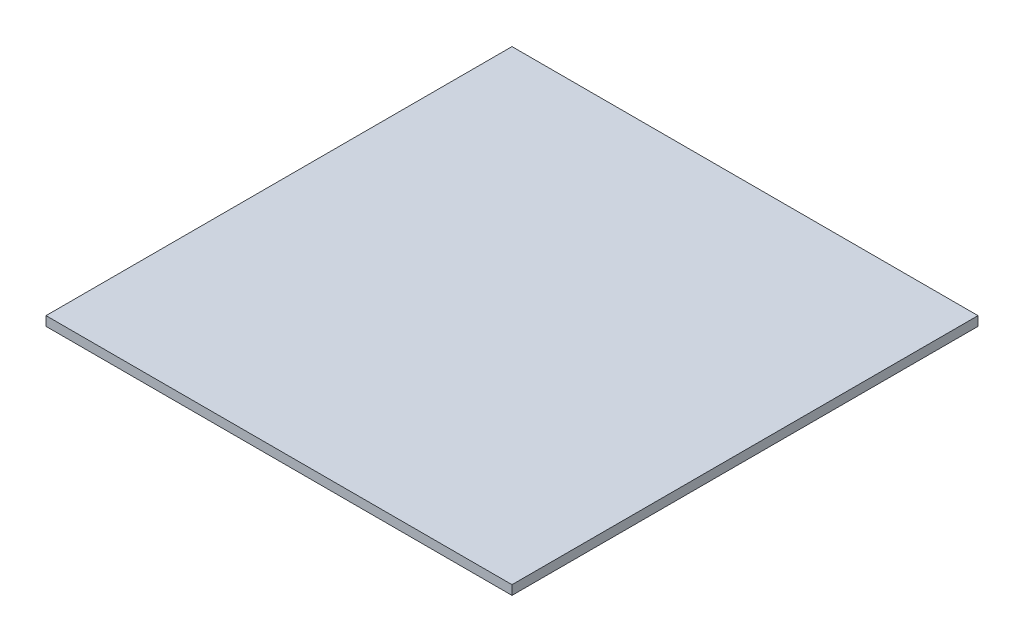
SolidWorks part; units mm, degrees
ref_plane "Vorne" through (0, 0, 0) normal (0, 0, 1) x (1, 0, 0)
ref_plane "Oben" through (0, 0, 0) normal (0, 1, 0) x (1, 0, 0)
ref_plane "Rechts" through (0, 0, 0) normal (1, 0, 0) x (0, 0, -1)
sketch "Skizze2" plane through (0, 0, 0) normal (0, 1, 0) x (1, 0, 0)
  line L1 (-500, -500) -> (500, -500)
  line L2 (-500, -500) -> (-500, 500)
  line L3 (-500, 500) -> (500, 500)
  line L4 (500, -500) -> (500, 500)
  line L5 (-500, -500) -> (500, 500) construction
  line L6 (-500, 500) -> (500, -500) construction
  point P0 (0, 0)
  dimension "D1" = 1000
  dimension "D2" = 1000
extrude "Aufsatz-Linear austragen1" add sketch "Skizze2" along normal blind 20
sketch "Skizze3" [suppressed] plane through (0, 20, 0) normal (0, 1, 0) x (1, 0, 0)
  line L8 (420, -420) -> (420, 420)
  line L9 (420, 420) -> (-420, 420)
  line L10 (-420, 420) -> (-420, -420)
  line L11 (-420, -420) -> (420, -420)
  line L12 (420, -420) -> (420, 420)
  line L13 (420, 420) -> (-420, 420)
  line L14 (-420, 420) -> (-420, -420)
  line L15 (-420, -420) -> (420, -420)
  dimension "D1" = 80
extrude "Schnitt-Linear austragen1" [suppressed] cut sketch "Skizze3" against normal blind 5 flip side to cut
sketch "Skizze6" [suppressed] plane through (0, 15, 0) normal (0, 1, 0) x (1, 0, 0)
  line L8 (450, -450) -> (450, 450)
  line L9 (450, 450) -> (-450, 450)
  line L10 (-450, 450) -> (-450, -450)
  line L11 (-450, -450) -> (450, -450)
  line L12 (450, -430) -> (450, 430)
  line L13 (430, 450) -> (-430, 450)
  line L14 (-450, 430) -> (-450, -430)
  line L15 (-430, -450) -> (430, -450)
  arc A0 (-450, -430) -> (-430, -450) centre (-430, -430) ccw
  arc A1 (450, -430) -> (430, -450) centre (430, -430) cw
  arc A2 (450, 430) -> (430, 450) centre (430, 430) ccw
  arc A3 (-430, 450) -> (-450, 430) centre (-430, 430) ccw
  dimension "D2" = 20
  dimension "D1" = 50
sketch "Skizze7" [suppressed] plane through (0, 0, 0) normal (0, 0, 1) x (1, 0, 0)
  line L0 (-454, 15) -> (-456.1031, 8.9911)
  line L1 (-500, 15) -> (500, 15) construction
  line L2 (-453.2716, 5) -> (-446.7284, 5)
  line L3 (-443.8969, 8.9911) -> (-446, 15)
  line L4 (-430, 15) -> (-450, 15) construction
  line L5 (-446, 15) -> (-454, 15)
  line L6 (-450, 15) -> (-450, 5) construction
  arc A0 (-446.7284, 5) -> (-443.8969, 8.9911) centre (-446.7284, 8) ccw
  arc A1 (-456.1031, 8.9911) -> (-453.2716, 5) centre (-453.2716, 8) ccw
  point P13 (-442.5, 5)
  point P16 (-457.5, 5)
  dimension "D4" = 3
  dimension "D1" = 10
  dimension "D2" = 15
  dimension "D3" = 8
sweep "Schnitt-Austragung1" [suppressed] cut profiles "Skizze7" path "Skizze6"
